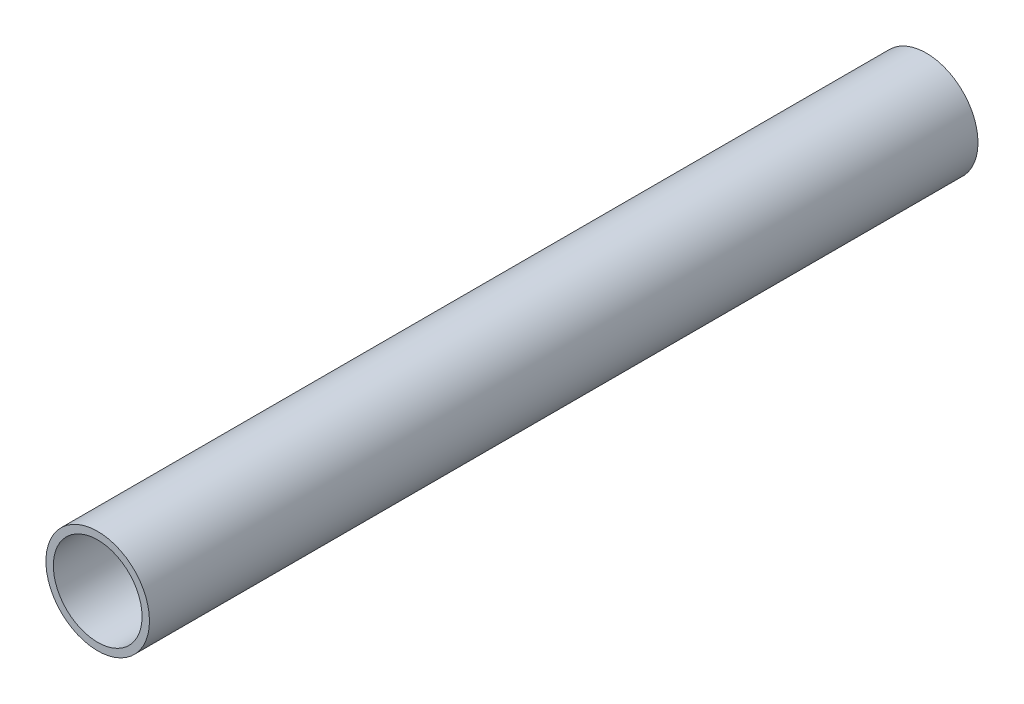
SolidWorks part; units mm, degrees
ref_plane "Front Plane" through (0, 0, 0) normal (0, 0, 1) x (1, 0, 0)
ref_plane "Top Plane" through (0, 0, 0) normal (0, 1, 0) x (1, 0, 0)
ref_plane "Right Plane" through (0, 0, 0) normal (1, 0, 0) x (0, 0, -1)
sketch "Sketch1" plane through (0, 0, 0) normal (0, 0, 1) x (1, 0, 0)
  circle A0 centre (0, 0) radius 3.175
  dimension "D1" = 6.35
extrude "Boss-Extrude1" add sketch "Sketch1" along normal blind 50.8
sketch "Sketch2" plane through (0, 0, 50.8) normal (0, 0, 1) x (1, 0, 0)
  circle A0 centre (0, 0) radius 2.7202
extrude "Cut-Extrude1" cut sketch "Sketch2" against normal blind 50.8
